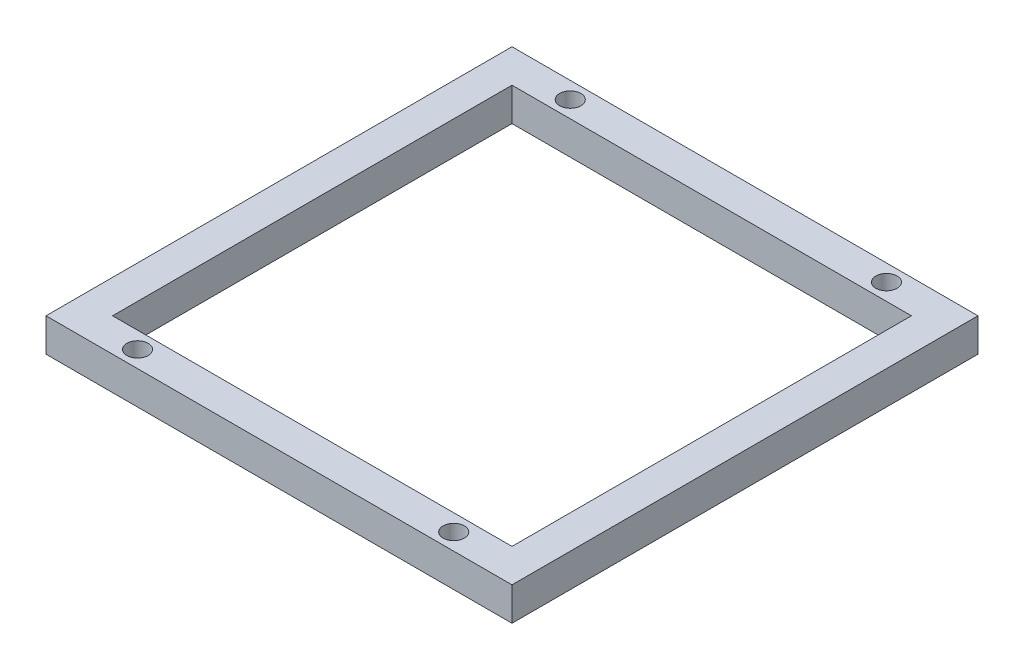
SolidWorks part; units mm, degrees
ref_plane "Front Plane" through (0, 0, 0) normal (0, 0, 1) x (1, 0, 0)
ref_plane "Top Plane" through (0, 0, 0) normal (0, 1, 0) x (1, 0, 0)
ref_plane "Right Plane" through (0, 0, 0) normal (1, 0, 0) x (0, 0, -1)
sketch "Sketch1" plane through (0, 0, 0) normal (0, 1, 0) x (1, 0, 0)
  line L0 (-30, 30) -> (30, 30)
  line L1 (-35, -35) -> (35, -35)
  line L2 (-35, -35) -> (-35, 35)
  line L3 (-35, 35) -> (35, 35)
  line L4 (35, -35) -> (35, 35)
  line L5 (-35, -35) -> (35, 35) construction
  line L6 (-35, 35) -> (35, -35) construction
  line L7 (30, -30) -> (30, 30)
  line L8 (-30, -30) -> (30, -30)
  line L9 (-30, -30) -> (-30, 30)
  line L11 (-23.75, -32.5) -> (23.75, -32.5) construction
  line L12 (-23.75, -32.5) -> (-23.75, 32.5) construction
  line L13 (-23.75, 32.5) -> (23.75, 32.5) construction
  line L14 (23.75, -32.5) -> (23.75, 32.5) construction
  line L15 (-23.75, -32.5) -> (23.75, 32.5) construction
  line L16 (-23.75, 32.5) -> (23.75, -32.5) construction
  circle A2 centre (-23.75, 32.5) radius 1.6
  circle A3 centre (23.75, 32.5) radius 1.6
  circle A4 centre (23.75, -32.5) radius 1.6
  circle A5 centre (-23.75, -32.5) radius 1.6
  point P0 (0, 0)
  point P10 (0, 0)
  dimension "D6" = 3.2
  dimension "D1" = 70
  dimension "D2" = 70
  dimension "D4" = 65
  dimension "D5" = 11.25
  dimension "D3" = 5
extrude "Boss-Extrude1" add sketch "Sketch1" along normal mid plane 5
